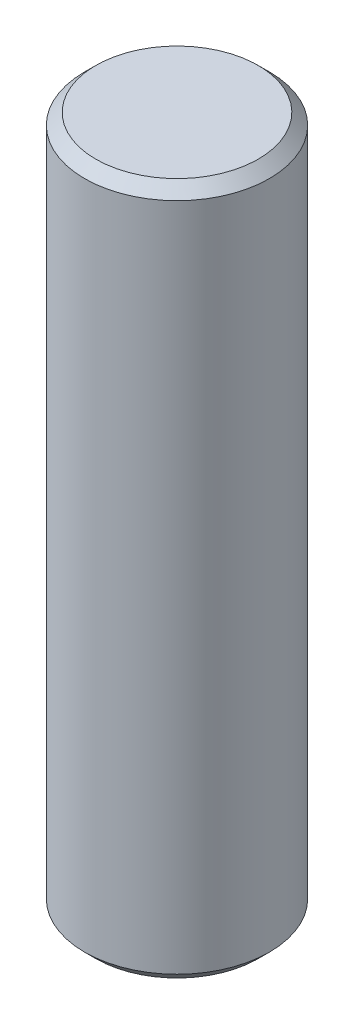
SolidWorks part; units mm, degrees
material "AISI 316 Stainless Steel Sheet (SS)"
ref_plane "Front" through (0, 0, 0) normal (0, 0, 1) x (1, 0, 0)
ref_plane "Top" through (0, 0, 0) normal (0, 1, 0) x (1, 0, 0)
ref_plane "Right" through (0, 0, 0) normal (1, 0, 0) x (0, 0, -1)
sketch "Sketch1" plane through (0, 0, 0) normal (0, 1, 0) x (1, 0, 0)
  circle A0 centre (0, 0) radius 4.125
  dimension "D1" = 8.25
extrude "Boss-Extrude1" add sketch "Sketch1" along normal blind 30.9
chamfer "Chamfer1" distance 0.5 angle 45 2 edges at (0, 0, 4.125) (0, 30.9, 4.125)
